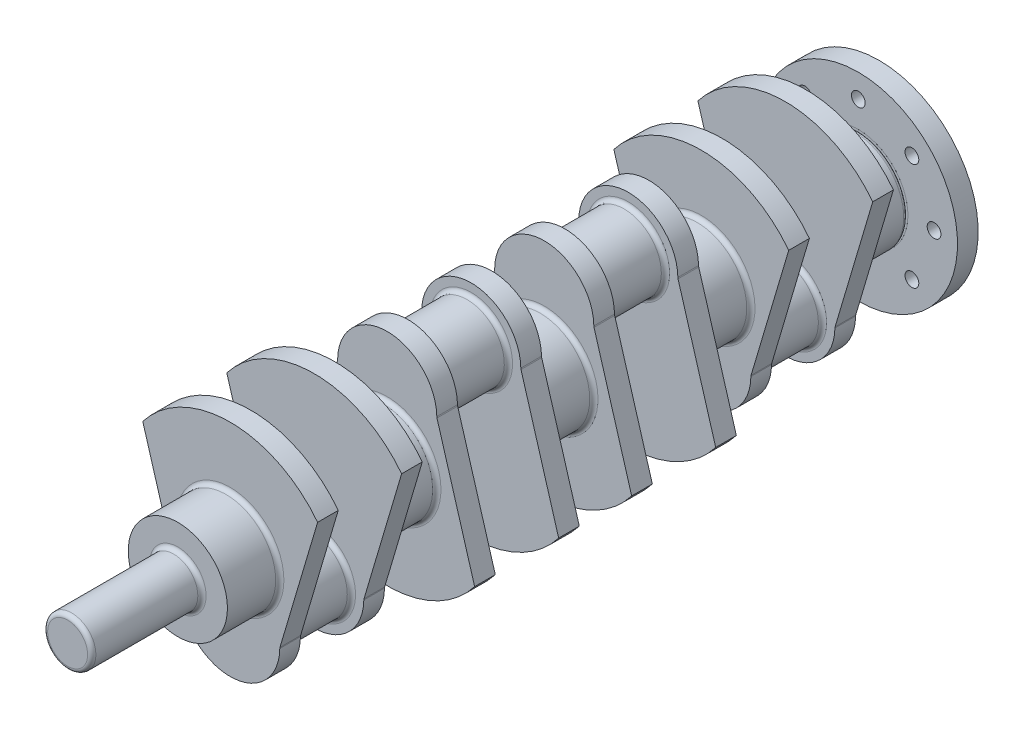
SolidWorks part; units mm, degrees
ref_plane "Front Plane" through (0, 0, 0) normal (0, 0, 1) x (1, 0, 0)
ref_plane "Top Plane" through (0, 0, 0) normal (0, 1, 0) x (1, 0, 0)
ref_plane "Right Plane" through (0, 0, 0) normal (1, 0, 0) x (0, 0, -1)
sketch "Sketch1" plane through (0, 0, 0) normal (0, 0, 1) x (1, 0, 0)
  line L0 (0, 104.7101) -> (0, -44) construction
  line L1 (-144.6741, 0) -> (110.2917, 0) construction
  line L2 (-63.4618, 48.7094) -> (-36, -44)
  line L3 (63.4618, 48.7094) -> (36, -44)
  circle A0 centre (0, -44) radius 36
  arc A1 (-63.4618, 48.7094) -> (63.4618, 48.7094) centre (0, 0) cw
  dimension "D1" = 72
  dimension "D3" = 80
  dimension "D2" = 33
  dimension "D4" = 44
extrude "Boss-Extrude1" add sketch "Sketch1" along normal blind 15 contours A1 L2 A0 L3 | A0
sketch "Sketch2" plane through (0, 0, 0) normal (0, 0, -1) x (-1, 0, 0)
  circle A1 centre (0, -44) radius 27
  dimension "D1" = 54
extrude "Boss-Extrude2" add sketch "Sketch2" along normal blind 46
sketch "Sketch3" plane through (0, 0, 15) normal (0, 0, 1) x (1, 0, 0)
  circle A0 centre (0, 0) radius 36
  dimension "D1" = 72
extrude "Boss-Extrude3" add sketch "Sketch3" along normal blind 38
ref_plane "Plane1" through (0, 0, 34) normal (0, 0, 1) x (1, 0, 0)
ref_plane "Plane4" through (0, 0, -23) normal (0, 0, -1) x (-1, 0, 0)
mirror "Mirror4" about plane through (0, 0, -23) normal (0, 0, -1) of "Boss-Extrude1", "Boss-Extrude3"
ref_plane "Plane5" through (0, 0, -80) normal (0, 0, -1) x (-1, 0, 0)
mirror "Mirror5" about plane through (0, 0, -80) normal (0, 0, -1) of bodies 110
move or copy body "Body-Move/Copy2" bodies to move or copy 111 copy no rotation origin (0, 0, -137) rotation axis (1, 0, 0) rotation angle 180
ref_plane "Plane6" through (0, 0, -194) normal (0, 0, -1) x (-1, 0, 0)
mirror "Mirror6" about plane through (0, 0, -194) normal (0, 0, -1) of bodies 112 110
sketch "Sketch6" plane through (0, 0, 53) normal (0, 0, 1) x (1, 0, 0)
  circle A0 centre (0, 0) radius 17.5
  dimension "D1" = 35
extrude "Boss-Extrude5" add sketch "Sketch6" along normal blind 80
sketch "Sketch7" plane through (0, 0, -441) normal (0, 0, -1) x (-1, 0, 0)
  circle A0 centre (0, 0) radius 55
  circle A1 centre (0, 0) radius 72
  circle A2 centre (0, 55) radius 5
  circle A3 centre (38.8909, 38.8909) radius 5
  circle A4 centre (55, 0) radius 5
  circle A5 centre (38.8909, -38.8909) radius 5
  circle A6 centre (0, -55) radius 5
  circle A7 centre (-38.8909, -38.8909) radius 5
  circle A8 centre (-55, 0) radius 5
  circle A9 centre (-38.8909, 38.8909) radius 5
  circle A10 centre (0, 0) radius 36 construction
  point P22 (0, 0)
  circle M3 centre (0, 0) radius 36
  dimension "D1" = 110
  dimension "D2" = 144
  dimension "D3" = 8
  dimension "D4" = 10
extrude "Boss-Extrude6" add sketch "Sketch7" along normal blind 15 separate body contours A9 A0 A8 A7 A6 A5 A4 A3 A2 M3 | A1 A9 A0 A2 A3 A4 A5 A6 A7 A8
combine bodies "Combine3" operation type add bodies to combine 114 113 112 115
fillet "Fillet1" radius 3 34 edges at (27, -44, -388) (-27, -44, -342) (36, 0, -403) (36, -44, -334.5) (-36, -44, -334.5) (36, 0, -289) (36, 0, -327) (-36, 44, -281.5) (36, 44, -281.5) (27, 44, -274) (36, 44, -220.5) (-36, 44, -220.5) (36, 0, -213) (-27, 44, -228) (36, 0, -175) (-36, 44, -106.5) (36, 44, -106.5) (36, 0, -99) (27, 44, -114) (-27, 44, -160) (36, 44, -167.5) (-36, 44, -167.5) (-36, -44, 7.5) (36, -44, 7.5) (27, -44, 0) (36, 0, 15) (36, -44, -53.5) (-36, -44, -53.5) (36, 0, -61) (-27, -44, -46) (17.5, 0, 53) (17.5, 0, 133) (36, -44, -395.5) (-36, -44, -395.5)
fillet "Fillet2" radius 3 1 edges at (36, 0, -441)
surface "Surface-Fill1"
